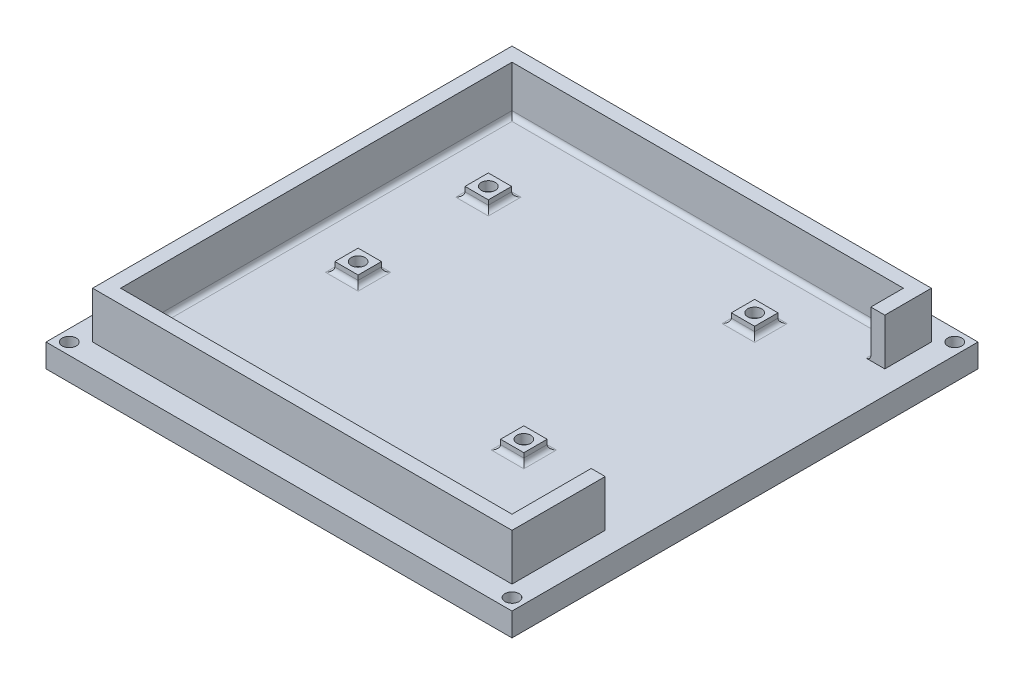
SolidWorks part; units mm, degrees
ref_plane "Front Plane" through (0, 0, 0) normal (0, 0, 1) x (1, 0, 0)
ref_plane "Top Plane" through (0, 0, 0) normal (0, 1, 0) x (1, 0, 0)
ref_plane "Right Plane" through (0, 0, 0) normal (1, 0, 0) x (0, 0, -1)
sketch "Sketch1" plane through (0, 0, 0) normal (0, 1, 0) x (1, 0, 0)
  line L1 (0, 0) -> (100, 0)
  line L2 (0, 0) -> (0, 100)
  line L3 (0, 100) -> (100, 100)
  line L4 (100, 0) -> (100, 100)
  dimension "D1" = 100
  dimension "D2" = 100
extrude "Boss-Extrude1" add sketch "Sketch1" along normal blind 5
sketch "Sketch2" plane through (0, 5, 0) normal (0, 1, 0) x (1, 0, 0)
  line L0 (100, 100) -> (0, 100) construction
  line L1 (5, 95) -> (95, 95)
  line L2 (5, 95) -> (5, 5)
  line L3 (5, 5) -> (95, 5)
  line L4 (95, 95) -> (95, 5)
  line L5 (100, 0) -> (100, 100) construction
  line L6 (0, 0) -> (100, 0) construction
  line L7 (0, 100) -> (0, 0) construction
  line L8 (8, 92) -> (92, 92)
  line L9 (92, 92) -> (92, 8)
  line L10 (8, 8) -> (92, 8)
  line L11 (8, 92) -> (8, 8)
  dimension "D1" = 5
  dimension "D2" = 5
  dimension "D3" = 5
  dimension "D4" = 5
  dimension "D5" = 3
extrude "Boss-Extrude2" add sketch "Sketch2" along normal blind 10
sketch "Sketch3" plane through (0, 5, 0) normal (0, 1, 0) x (1, 0, 0)
  line L0 (8, 92) -> (8, 8) construction
  line L1 (18, 82) -> (86.58, 82)
  line L2 (18, 82) -> (18, 28.66)
  line L3 (18, 28.66) -> (86.58, 28.66)
  line L4 (86.58, 82) -> (86.58, 28.66)
  line L5 (92, 92) -> (8, 92) construction
  circle A0 centre (72.61, 79.46) radius 1.5
  circle A1 centre (71.34, 31.2) radius 1.5
  circle A2 centre (20.54, 74.38) radius 1.5
  circle A3 centre (20.54, 46.44) radius 1.5
  dimension "D5" = 3
  dimension "D6" = 2.54
  dimension "D7" = 13.97
  dimension "D8" = 3
  dimension "D9" = 2.54
  dimension "D10" = 15.24
  dimension "D11" = 3
  dimension "D12" = 2.54
  dimension "D13" = 7.62
  dimension "D14" = 3
  dimension "D15" = 2.54
  dimension "D16" = 27.94
  dimension "D1" = 68.58
  dimension "D2" = 53.34
  dimension "D3" = 10
  dimension "D4" = 10
sketch "Sketch4" plane through (0, 5, 0) normal (0, 1, 0) x (1, 0, 0)
  line L0 (18.04, 48.94) -> (23.04, 48.94)
  line L1 (18.04, 76.88) -> (23.04, 76.88)
  line L2 (18.04, 76.88) -> (18.04, 71.88)
  line L3 (18.04, 71.88) -> (23.04, 71.88)
  line L4 (23.04, 76.88) -> (23.04, 71.88)
  line L5 (18.04, 76.88) -> (23.04, 71.88) construction
  line L6 (18.04, 71.88) -> (23.04, 76.88) construction
  line L7 (18.04, 48.94) -> (18.04, 43.94)
  line L8 (18.04, 43.94) -> (23.04, 43.94)
  line L9 (23.04, 48.94) -> (23.04, 43.94)
  line L10 (18.04, 48.94) -> (23.04, 43.94) construction
  line L11 (18.04, 43.94) -> (23.04, 48.94) construction
  line L13 (70.11, 81.96) -> (75.11, 81.96)
  line L14 (70.11, 81.96) -> (70.11, 76.96)
  line L15 (70.11, 76.96) -> (75.11, 76.96)
  line L16 (75.11, 81.96) -> (75.11, 76.96)
  line L17 (70.11, 81.96) -> (75.11, 76.96) construction
  line L18 (70.11, 76.96) -> (75.11, 81.96) construction
  line L19 (68.84, 33.7) -> (73.84, 33.7)
  line L20 (68.84, 33.7) -> (68.84, 28.7)
  line L21 (68.84, 28.7) -> (73.84, 28.7)
  line L22 (73.84, 33.7) -> (73.84, 28.7)
  line L23 (68.84, 33.7) -> (73.84, 28.7) construction
  line L24 (68.84, 28.7) -> (73.84, 33.7) construction
  circle A0 centre (20.54, 74.38) radius 1.5
  circle A1 centre (20.54, 46.44) radius 1.5
  circle A2 centre (72.61, 79.46) radius 1.5
  circle A3 centre (71.34, 31.2) radius 1.5
  point P0 (20.54, 74.38)
  point P8 (72.61, 79.46)
  point P10 (20.54, 46.44)
  dimension "D1" = 5
  dimension "D2" = 5
  dimension "D4" = 5
  dimension "D5" = 5
  dimension "D6" = 5
  dimension "D7" = 5
  dimension "D3" = 2
extrude "Boss-Extrude3" add sketch "Sketch4" along normal blind 2
fillet "Fillet1" radius 1 20 edges at (92, 5, -50) (50, 5, -8) (8, 5, -50) (50, 5, -92) (20.54, 5, -76.88) (18.04, 5, -74.38) (20.54, 5, -71.88) (23.04, 5, -74.38) (72.61, 5, -81.96) (70.11, 5, -79.46) (72.61, 5, -76.96) (75.11, 5, -79.46) (20.54, 5, -48.94) (18.04, 5, -46.44) (20.54, 5, -43.94) (23.04, 5, -46.44) (71.34, 5, -33.7) (68.84, 5, -31.2) (71.34, 5, -28.7) (73.84, 5, -31.2)
sketch "Sketch5" plane through (95, 0, 0) normal (1, 0, 0) x (0, 0, -1)
  line L0 (5, 15) -> (95, 15) construction
  line L1 (25, 15) -> (85, 15)
  line L2 (25, 15) -> (25, 5)
  line L3 (25, 5) -> (85, 5)
  line L4 (85, 15) -> (85, 5)
  line L5 (5, 5) -> (95, 5) construction
  line L6 (95, 15) -> (95, 5) construction
  dimension "D1" = 60
  dimension "D2" = 10
extrude "Cut-Extrude1" cut sketch "Sketch5" against normal blind 5
sketch "Sketch6" plane through (0, 0, 0) normal (0, -1, 0) x (1, 0, 0)
  line L0 (0, 0) -> (100, 0) construction
  line L1 (0, -100) -> (0, 0) construction
  circle A0 centre (2.5, -2.5) radius 1.5
  dimension "D1" = 3
  dimension "D2" = 2.5
  dimension "D3" = 2.5
extrude "Cut-Extrude2" cut sketch "Sketch6" against normal blind 5
pattern_linear "LPattern1" count 2 spacing 95 along (1, 0, 0) count 2 spacing 95 along (0, 0, -1) of "Cut-Extrude2"
